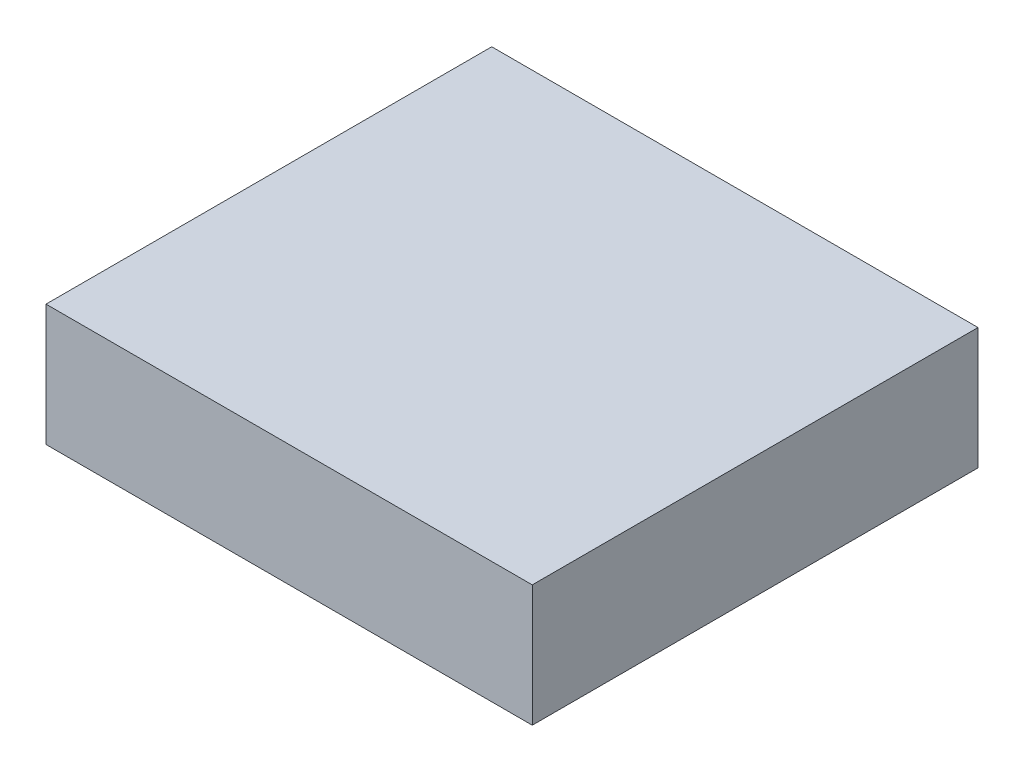
SolidWorks part; units mm, degrees
ref_plane "Front Plane" through (0, 0, 0) normal (0, 0, 1) x (1, 0, 0)
ref_plane "Top Plane" through (0, 0, 0) normal (0, 1, 0) x (1, 0, 0)
ref_plane "Right Plane" through (0, 0, 0) normal (1, 0, 0) x (0, 0, -1)
sketch "Sketch1" plane through (0, 0, 0) normal (0, 1, 0) x (1, 0, 0)
  line L1 (0, 0) -> (152.4, 0)
  line L2 (0, 0) -> (0, 139.7)
  line L3 (0, 139.7) -> (152.4, 139.7)
  line L4 (152.4, 0) -> (152.4, 139.7)
  dimension "D1" = 139.7
  dimension "D2" = 152.4
extrude "Boss-Extrude1" add sketch "Sketch1" along normal blind 38.1
